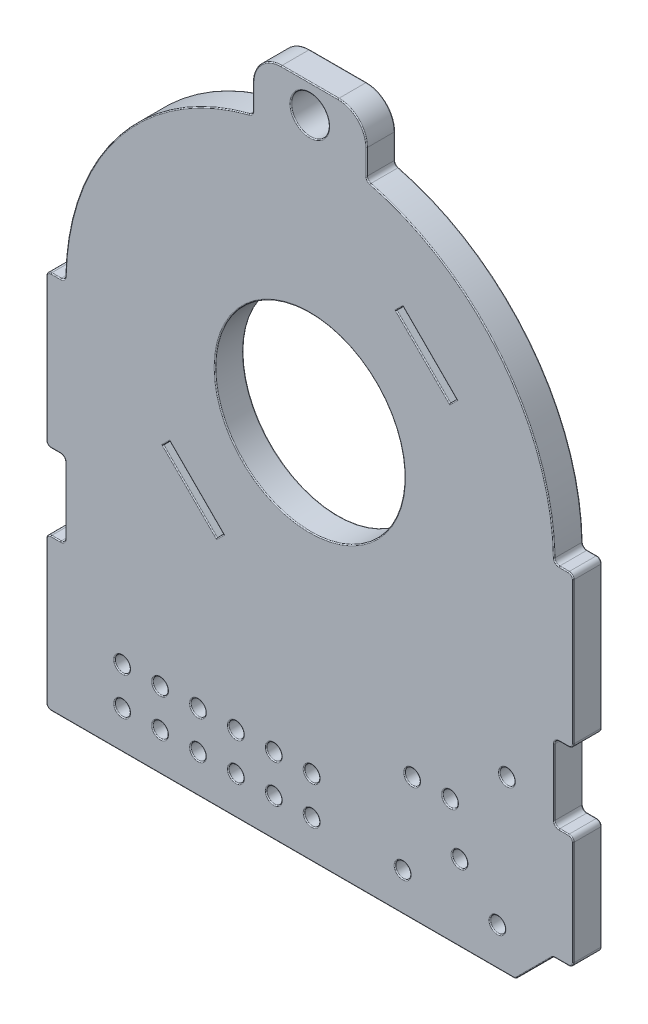
SolidWorks part; units mm, degrees
ref_plane "Ön Düzlem" through (0, 0, 0) normal (0, 0, 1) x (1, 0, 0)
ref_plane "Üst Düzlem" through (0, 0, 0) normal (0, 1, 0) x (1, 0, 0)
ref_plane "Sağ Düzlem" through (0, 0, 0) normal (1, 0, 0) x (0, 0, -1)
sketch "Sketch1" plane through (0, 0, 0) normal (0, 0, 1) x (1, 0, 0)
  line L0 (13.1476, 0) -> (13.65, 0)
  line L1 (-13.65, 0) -> (-13.1476, 0)
  line L2 (-13.9, -0.25) -> (-13.9, -7.75)
  line L3 (-13.65, -20) -> (10.7418, -20)
  line L4 (13.9, -0.25) -> (13.9, -7.75)
  line L5 (0, 15.5463) -> (0, 12.9) construction
  line L6 (-3, 12.7421) -> (-3, 14.0463)
  line L7 (0, -20) -> (0, 12.9) construction
  line L8 (12.7722, -18.0732) -> (10.9186, -19.9268)
  line L9 (13.65, -18) -> (12.949, -18)
  line L10 (13.9, -12.25) -> (13.9, -17.75)
  line L11 (13.65, -8) -> (13.15, -8)
  line L12 (-13.65, -12) -> (-13.15, -12)
  line L13 (13.65, -12) -> (13.15, -12)
  line L14 (12.9, -8.25) -> (12.9, -11.75)
  line L15 (-12.9, -8.25) -> (-12.9, -11.75)
  line L16 (-13.65, -8) -> (-13.15, -8)
  line L17 (-13.9, -12.25) -> (-13.9, -19.75)
  line L18 (-1.5, 15.5463) -> (1.5, 15.5463)
  line L19 (3, 14.0463) -> (3, 12.7421)
  line L20 (3, 14.0463) -> (-3, 14.0463) construction
  arc A0 (12.8977, 0.2452) -> (3.1882, 12.4998) centre (0, 0) ccw
  arc A1 (-12.8977, 0.2452) -> (-13.1476, 0) centre (-13.1476, 0.25) cw
  arc A2 (-13.65, 0) -> (-13.9, -0.25) centre (-13.65, -0.25) ccw
  arc A3 (12.8977, 0.2452) -> (13.1476, 0) centre (13.1476, 0.25) ccw
  arc A4 (13.65, 0) -> (13.9, -0.25) centre (13.65, -0.25) cw
  arc A5 (13.65, -18) -> (13.9, -17.75) centre (13.65, -17.75) ccw
  arc A6 (12.7722, -18.0732) -> (12.949, -18) centre (12.949, -18.25) cw
  arc A7 (10.9186, -19.9268) -> (10.7418, -20) centre (10.7418, -19.75) cw
  arc A8 (-13.65, -20) -> (-13.9, -19.75) centre (-13.65, -19.75) cw
  arc A9 (-3.1882, 12.4998) -> (-12.8977, 0.2452) centre (0, 0) ccw
  arc A10 (-3.1882, 12.4998) -> (-3, 12.7421) centre (-3.25, 12.7421) ccw
  circle A11 centre (0, 0) radius 12.9 construction
  arc A12 (-13.65, -8) -> (-13.9, -7.75) centre (-13.65, -7.75) cw
  arc A13 (-13.65, -12) -> (-13.9, -12.25) centre (-13.65, -12.25) ccw
  arc A14 (-13.15, -12) -> (-12.9, -11.75) centre (-13.15, -11.75) ccw
  arc A15 (-12.9, -8.25) -> (-13.15, -8) centre (-13.15, -8.25) ccw
  arc A16 (13.15, -8) -> (12.9, -8.25) centre (13.15, -8.25) ccw
  arc A17 (13.65, -8) -> (13.9, -7.75) centre (13.65, -7.75) ccw
  arc A18 (13.15, -12) -> (12.9, -11.75) centre (13.15, -11.75) cw
  arc A19 (13.9, -12.25) -> (13.65, -12) centre (13.65, -12.25) ccw
  circle A20 centre (10.4, -11) radius 0.4
  circle A21 centre (7.9, -16) radius 0.4
  circle A22 centre (9.9, -18) radius 0.4
  circle A23 centre (4.9, -18) radius 0.4
  circle A24 centre (7.4, -13.5) radius 0.4
  circle A25 centre (5.4, -13.5) radius 0.4
  arc A26 (3.1882, 12.4998) -> (3, 12.7421) centre (3.25, 12.7421) cw
  arc A27 (-3, 14.0463) -> (-1.5, 15.5463) centre (-1.5, 14.0463) cw
  arc A28 (1.5, 15.5463) -> (3, 14.0463) centre (1.5, 14.0463) cw
  circle A29 centre (0, 14.0463) radius 1
  circle A30 centre (0.1, -18) radius 0.4
  circle A31 centre (-1.9, -18) radius 0.4
  circle A32 centre (-3.9, -18) radius 0.4
  circle A33 centre (-5.9, -18) radius 0.4
  circle A34 centre (-7.9, -18) radius 0.4
  circle A35 centre (-9.9, -18) radius 0.4
  circle A36 centre (-1.9, -16) radius 0.4
  circle A37 centre (-3.9, -16) radius 0.4
  circle A38 centre (-5.9, -16) radius 0.4
  circle A39 centre (-7.9, -16) radius 0.4
  circle A40 centre (-9.9, -16) radius 0.4
  circle A41 centre (0.1, -16) radius 0.4
  point P18 (-13.9, 0)
  point P21 (12.9, 0)
  point P26 (13.9, -18)
  point P29 (12.8454, -18)
  point P32 (10.8454, -20)
  point P39 (-3, 12.5463)
  point P53 (-13.9, -8)
  point P56 (-13.9, -12)
  point P59 (-12.9, -12)
  point P62 (-12.9, -8)
  point P65 (12.9, -8)
  point P68 (13.9, -8)
  point P71 (12.9, -12)
  point P74 (13.9, -12)
  point P87 (3, 12.5463)
  point P92 (3, 15.5463)
  dimension "D1" = 25.8
  dimension "D4" = 0.25
  dimension "D11" = 0.25
  dimension "D12" = 0.8
  dimension "D13" = 2.5
  dimension "D14" = 9
  dimension "D15" = 0.8
  dimension "D16" = 0.8
  dimension "D17" = 0.8
  dimension "D18" = 2
  dimension "D19" = 2
  dimension "D20" = 5
  dimension "D21" = 4
  dimension "D22" = 4
  dimension "D23" = 2
  dimension "D24" = 0.8
  dimension "D25" = 0.8
  dimension "D26" = 2
  dimension "D27" = 6.5
  dimension "D28" = 0
  dimension "D5" = 0.25
  dimension "D29" = 0.25
  dimension "D30" = 1.5
  dimension "D32" = 2
  dimension "D33" = 0.8
  dimension "D36" = 2
  dimension "D37" = 4
  dimension "D38" = 6.5
  dimension "D2" = 13.9
  dimension "D3" = 13.9
  dimension "D6" = 3
  dimension "D7" = 3
  dimension "D8" = 8
  dimension "D9" = 4
  dimension "D10" = 1
  dimension "D31" = 1.5
  dimension "D35" = 6
  dimension "D34" = 2
extrude "Boss-Extrude1" add sketch "Sketch1" along normal blind 1.5
sketch "Sketch2" plane through (0, 0, 1.5) normal (0, 0, 1) x (1, 0, 0)
  line L0 (-12.9, 0) -> (12.9, 0) construction
  line L2 (4.5608, 7.3893) -> (4.9144, 7.7428)
  line L3 (7.3893, 4.5608) -> (4.5608, 7.3893)
  line L4 (7.7428, 4.9144) -> (7.3893, 4.5608)
  line L5 (-9.1217, -9.1217) -> (9.0267, 9.0267) construction
  line L6 (4.9144, 7.7428) -> (7.7428, 4.9144)
  line L10 (-7.7428, -4.9144) -> (-4.9144, -7.7428)
  line L11 (-4.9144, -7.7428) -> (-4.5608, -7.3893)
  line L12 (-4.5608, -7.3893) -> (-7.3893, -4.5608)
  line L13 (-7.3893, -4.5608) -> (-7.7428, -4.9144)
  circle A0 centre (0, 0) radius 5
  circle A1 centre (0, 0) radius 12.9 construction
  dimension "D1" = 10
  dimension "D2" = 16.9
  dimension "D3" = 8.45
  dimension "D6" = 4
  dimension "D7" = 0.5
  dimension "D8" = 2
  dimension "D10" = 45
  dimension "D11" = 0
extrude "Cut-Extrude1" cut sketch "Sketch2" against normal through all
fillet "Fillet1" radius 0.05 54 edges at (10.111, 8.0111, 0) (5, 0, 0) (7.566, 4.7376, 1.5) (6.3286, 6.3286, 1.5) (4.7376, 7.566, 1.5) (5.9751, 5.9751, 1.5) (-6.3286, -6.3286, 1.5) (-5.9751, -5.9751, 1.5) (-7.566, -4.7376, 1.5) (13.3988, 0, 0) (-13.3988, 0, 0) (-13.9, -4, 0) (-13.3988, 0, 1.5) (11.8454, -19, 0) (-13.8268, -0.0732, 0) (12.8533, -18.019, 0) (-12.9725, 0.0716, 0) (13.8268, -17.9268, 1.5) (12.8533, -18.019, 1.5) (-12.9725, 0.0716, 1.5) (-13.4, -8, 0) (-12.9, -10, 0) (-13.9, -16, 0) (13.4, -12, 0) (12.9, -10, 0) (13.4, -8, 0) (13.4, -12, 1.5) (-13.4, -12, 1.5) (-12.9732, -8.0732, 0) (12.9732, -11.9268, 0) (13.8268, -7.9268, 0) (10.8, -11, 1.5) (13.8268, -7.9268, 1.5) (12.9732, -8.0732, 1.5) (12.9732, -11.9268, 1.5) (-12.9732, -11.9268, 1.5) (-12.9732, -8.0732, 1.5) (10.3, -18, 1.5) (5.8, -13.5, 1.5) (-13.8268, -19.9268, 0) (-13.8268, -19.9268, 1.5) (3.0526, 12.5887, 0) (3, 13.3942, 0) (0, 15.5463, 0) (-3, 13.3942, 0) (-10.111, 8.0111, 1.5) (-3.0526, 12.5887, 1.5) (2.5607, 15.107, 1.5) (3, 13.3942, 1.5) (-7.5, -16, 1.5) (0.5, -18, 1.5) (-7.5, -18, 1.5) (-1.5, -16, 1.5) (-9.5, -16, 1.5)
